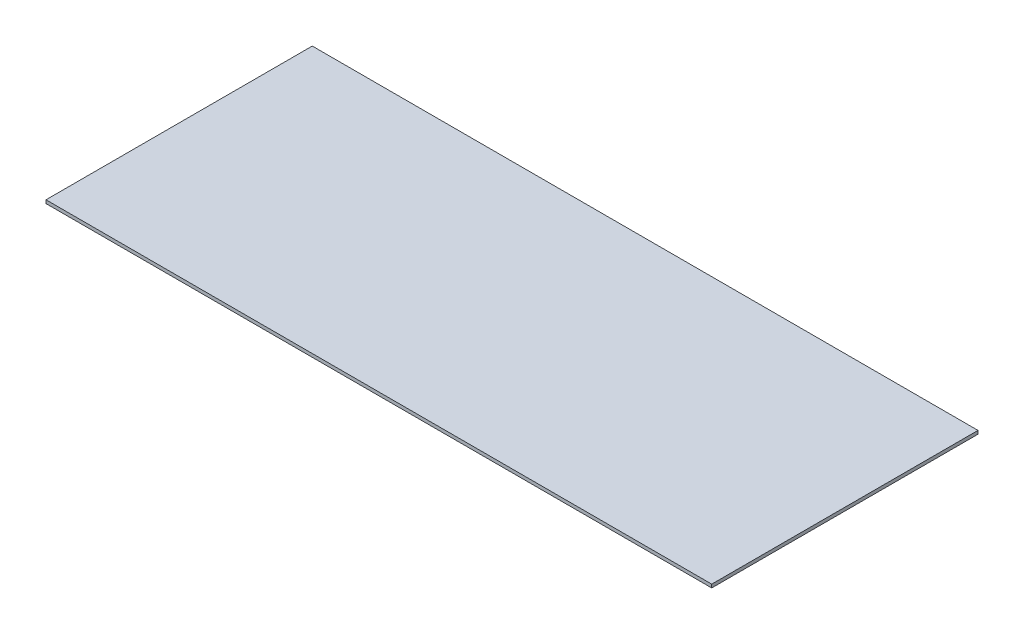
SolidWorks part; units mm, degrees
material "普通碳钢"
ref_plane "前视基准面" through (0, 0, 0) normal (0, 0, 1) x (1, 0, 0)
ref_plane "上视基准面" through (0, 0, 0) normal (0, 1, 0) x (1, 0, 0)
ref_plane "右视基准面" through (0, 0, 0) normal (1, 0, 0) x (0, 0, -1)
sketch "草图1" plane through (0, 0, 0) normal (0, 1, 0) x (1, 0, 0)
  line L1 (-100, 40) -> (100, 40)
  line L2 (-100, 40) -> (-100, -40)
  line L3 (-100, -40) -> (100, -40)
  line L4 (100, 40) -> (100, -40)
  dimension "D1" = 200
  dimension "D2" = 80
  dimension "D3" = 40
  dimension "D4" = 100
extrude "凸台-拉伸1" add sketch "草图1" along normal blind 1
